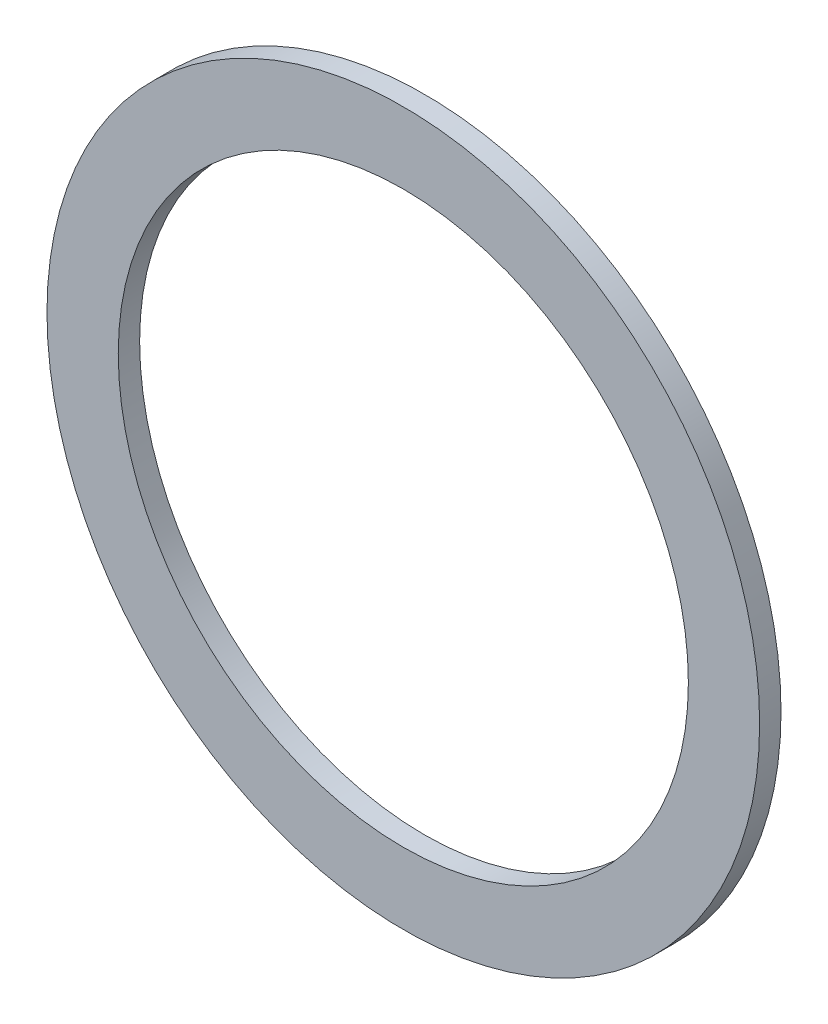
SolidWorks part; units mm, degrees
ref_plane "Front Plane" through (0, 0, 0) normal (0, 0, 1) x (1, 0, 0)
ref_plane "Top Plane" through (0, 0, 0) normal (0, 1, 0) x (1, 0, 0)
ref_plane "Right Plane" through (0, 0, 0) normal (1, 0, 0) x (0, 0, -1)
sketch "Sketch1" plane through (0, 0, 0) normal (0, 0, 1) x (1, 0, 0)
  circle A0 centre (0, 0) radius 1.6667
  circle A1 centre (0, 0) radius 1
  dimension "D1" = 2
extrude "Boss-Extrude1" add sketch "Sketch1" along normal blind 0.075
sketch "Sketch2" plane through (0, 0, 0.075) normal (0, 0, 1) x (1, 0, 0)
  circle A0 centre (0, 0) radius 1.25
  circle A1 centre (0, 0) radius 1.8696
  dimension "D1" = 2.5
extrude "Cut-Extrude1" cut sketch "Sketch2" against normal blind 10
